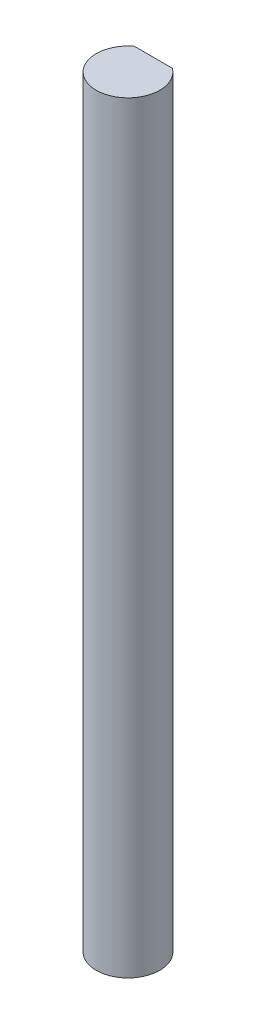
SolidWorks part; units mm, degrees
ref_plane "Front Plane" through (0, 0, 0) normal (0, 0, 1) x (1, 0, 0)
ref_plane "Top Plane" through (0, 0, 0) normal (0, 1, 0) x (1, 0, 0)
ref_plane "Right Plane" through (0, 0, 0) normal (1, 0, 0) x (0, 0, -1)
sketch "Sketch1" plane through (0, 0, 0) normal (0, 1, 0) x (1, 0, 0)
  line L0 (-1.905, 2.54) -> (1.905, 2.54)
  arc A0 (-1.905, 2.54) -> (1.905, 2.54) centre (0, 0) ccw
  dimension "D1" = 6.35
  dimension "D2" = 2.54
extrude "Boss-Extrude1" add sketch "Sketch1" along normal blind 76.2
